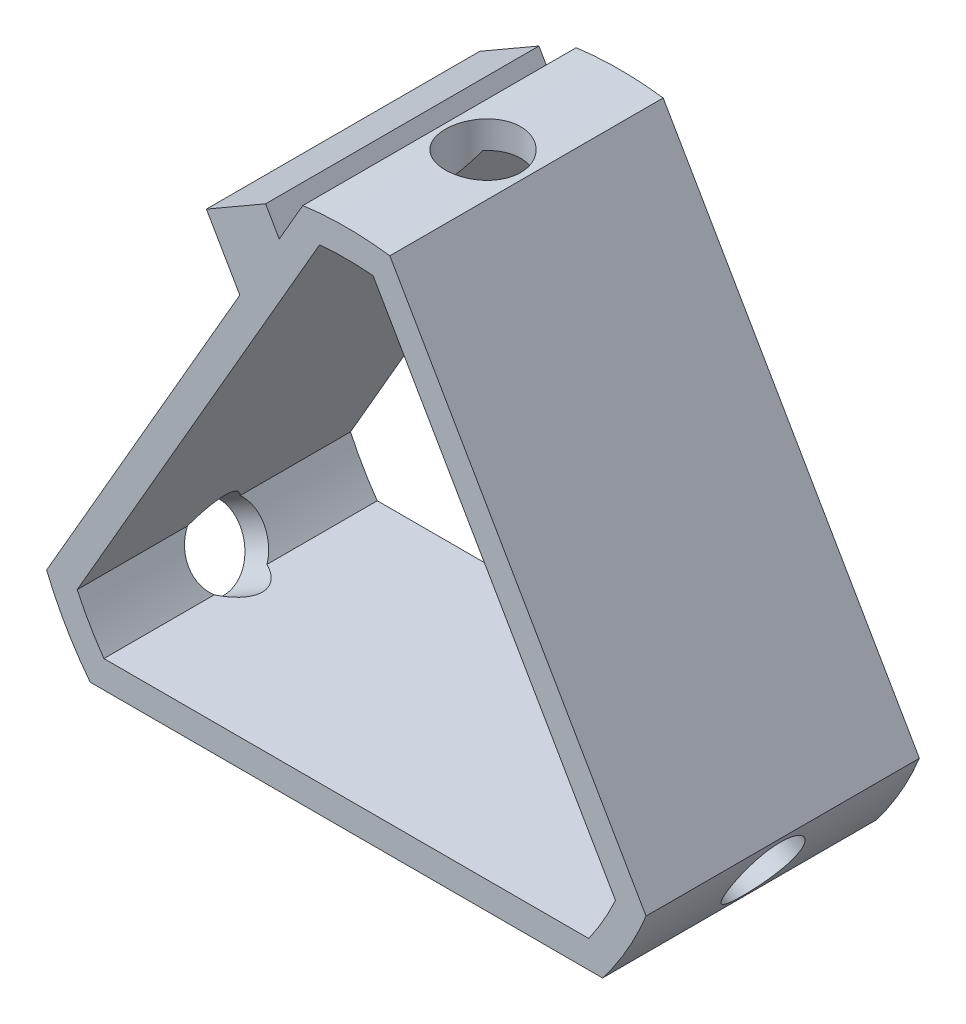
SolidWorks part; units mm, degrees
material "ABS"
ref_plane "Plan de face" through (0, 0, 0) normal (0, 0, 1) x (1, 0, 0)
ref_plane "Plan de dessus" through (0, 0, 0) normal (0, 1, 0) x (1, 0, 0)
ref_plane "Plan de droite" through (0, 0, 0) normal (1, 0, 0) x (0, 0, -1)
sketch "Esquisse1" plane through (0, 0, 0) normal (0, 0, 1) x (1, 0, 0)
  line L0 (0, 0) -> (0, 21.7) construction
  line L1 (0, 0) -> (-19.6944, -9.1116) construction
  line L2 (0, 0) -> (-17.7381, -12.5) construction
  line L3 (-18.7928, -10.85) -> (0, 0) construction
  line L4 (0, 0) -> (17.7381, -12.5) construction
  line L5 (18.7928, -10.85) -> (0, 0) construction
  line L6 (0, 0) -> (19.6944, -9.1116) construction
  line L7 (0, 0) -> (-1.9563, 21.6116) construction
  line L8 (0, 0) -> (1.9563, 21.6116) construction
  line L9 (37.4454, -12.5) -> (-34.2031, -12.5) construction
  line L10 (-21.6506, -12.5) -> (2.5161, 29.358) construction
  line L11 (0, 0) -> (-18.7928, -10.85) construction
  line L12 (21.6506, -12.5) -> (0, 25) construction
  line L13 (0, 0) -> (0, -19) construction
  line L14 (19.6944, -9.1116) -> (1.9563, 21.6116)
  line L15 (-36, -19) -> (36, -19)
  line L16 (-36, -19) -> (-36, -29)
  line L17 (-36, -29) -> (36, -29)
  line L18 (36, -19) -> (36, -29)
  line L19 (-1.9563, 21.6116) -> (-19.6944, -9.1116)
  line L20 (-17.7381, -12.5) -> (17.7381, -12.5)
  line L21 (-3.184, 23.4851) -> (-21.9307, -8.9851)
  line L22 (-18.7467, -14.5) -> (18.7467, -14.5)
  line L23 (21.9307, -8.9851) -> (3.184, 23.4851)
  line L24 (0, 0) -> (32.9548, -19) construction
  circle A1 centre (0, 0) radius 12.5
  arc A2 (-17.7381, -12.5) -> (-19.6944, -9.1116) centre (0, 0) cw
  arc A3 (-1.9563, 21.6116) -> (1.9563, 21.6116) centre (0, 0) cw
  arc A4 (17.7381, -12.5) -> (19.6944, -9.1116) centre (0, 0) ccw
  arc A5 (-18.7467, -14.5) -> (-21.9307, -8.9851) centre (0, 0) cw
  arc A6 (18.7467, -14.5) -> (21.9307, -8.9851) centre (0, 0) ccw
  arc A7 (-3.184, 23.4851) -> (3.184, 23.4851) centre (0, 0) cw
  dimension "D6" = 6.5
  dimension "D11" = 25
  dimension "D7" = 120
  dimension "D4" = 72
  dimension "D2" = 60
  dimension "D3" = 60
  dimension "D5" = 10
  dimension "D8" = 120
  dimension "D9" = 21.7
  dimension "D10" = 21.7
  dimension "D12" = 21.7
  dimension "D13" = 21.7
  dimension "D14" = 21.7
  dimension "D15" = 21.7
  dimension "D16" = 21.7
  dimension "D17" = 21.7
  dimension "D18" = 21.7
  dimension "D19" = 2
extrude "Boss.-Extru.1" add sketch "Esquisse1" along normal mid plane 20 contours A7 L21 A5 L22 A6 L23 A4 L20 A2 L19 A3 L14
ref_plane "Plan1" through (-20.3387, -11.7426, 0) normal (-0.866, -0.5, 0) x (0, 0, 1)
ref_plane "Plan2" through (0, 23.4851, 0) normal (0, -1, 0) x (-1, 0, 0)
ref_plane "Plan3" through (20.3387, -11.7426, 0) normal (-0.866, 0.5, 0) x (0, 0, 1)
sketch "Esquisse2" plane through (20.3387, -11.7426, 0) normal (-0.866, 0.5, 0) x (0, 0, 1)
  circle A0 centre (0, 0) radius 2.75
  dimension "D1" = 5.5
extrude "Enlèv. mat.-Extru.1" cut sketch "Esquisse2" against normal mid plane 20
sketch "Esquisse3" plane through (-20.3387, -11.7426, 0) normal (-0.866, -0.5, 0) x (0, 0, 1)
  circle A0 centre (0, 0) radius 2.75
  dimension "D1" = 5.5
extrude "Enlèv. mat.-Extru.2" cut sketch "Esquisse3" against normal mid plane 20
sketch "Esquisse4" plane through (0, 23.4851, 0) normal (0, -1, 0) x (-1, 0, 0)
  circle A0 centre (0, 0) radius 2.75
  dimension "D1" = 5.5
extrude "Enlèv. mat.-Extru.3" cut sketch "Esquisse4" against normal mid plane 20
sketch "Esquisse6" plane through (0, 0, -10) normal (0, 0, -1) x (-1, 0, 0)
  line L1 (1.9563, 21.6116) -> (19.6944, -9.1116) construction
  line L2 (3.184, 23.4851) -> (21.9307, -8.9851) construction
  line L4 (-19.6944, -9.1116) -> (-1.9563, 21.6116) construction
  line L5 (14.3101, 0.2142) -> (20.0836, -9.7858)
  line L6 (4.9075, 20.5) -> (5.9075, 22.2321)
  line L7 (5.9075, 22.2321) -> (10.2376, 19.7321)
  line L8 (7.7942, 15.5) -> (10.2376, 19.7321)
  line L9 (4.9075, 20.5) -> (7.7942, 15.5)
  line L10 (4.9075, 20.5) -> (9.2376, 18) construction
  line L11 (17.7381, -12.5) -> (19.6944, -9.1116) construction
  line L13 (-9.5102, -14.4722) -> (18.8179, 34.5935) construction
  line M7 (21.9307, -8.9851) -> (3.184, 23.4851)
  dimension "D1" = 5
  dimension "D2" = 5
  dimension "D3" = 11.5
  dimension "D4" = 2
extrude "Boss.-Extru.4" add sketch "Esquisse6" against normal up to surface (20 mm away) contours L10 L8 M7 | L6 L10 L8 L7 up to face at (0, 0, 10)
sketch "Esquisse7" plane through (0, 0, 10) normal (0, 0, 1) x (1, 0, 0)
  line L0 (0, 23.7) -> (0, 21.7) construction
  line L1 (0, 21.7) -> (0, 0) construction
  arc A0 (3.184, 23.4851) -> (-3.184, 23.4851) centre (0, 0) ccw construction
  arc A1 (1.9563, 21.6116) -> (-1.9563, 21.6116) centre (0, 0) ccw construction
